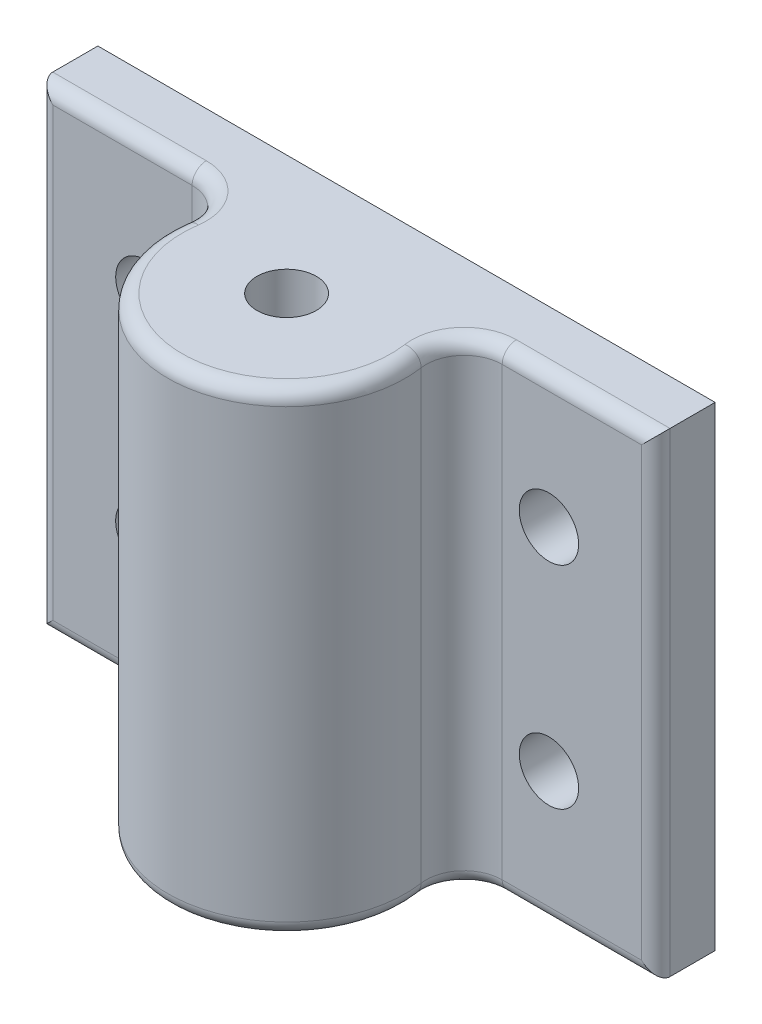
SolidWorks part; units mm, degrees
material "ABS"
ref_plane "Front Plane" through (0, 0, 0) normal (0, 0, 1) x (1, 0, 0)
ref_plane "Top Plane" through (0, 0, 0) normal (0, 1, 0) x (1, 0, 0)
ref_plane "Right Plane" through (0, 0, 0) normal (1, 0, 0) x (0, 0, -1)
sketch "Sketch1" plane through (0, 0, 0) normal (0, 1, 0) x (1, 0, 0)
  circle A0 centre (0, 0) radius 6.35
  dimension "D1" = 12.7
extrude "Boss-Extrude1" add sketch "Sketch1" along normal mid plane 25.4
sketch "Sketch2" plane through (0, -12.7, 0) normal (0, -1, 0) x (1, 0, 0)
  line L0 (0, 0) -> (0, -3.6102) construction
  line L1 (16.51, -3.2385) -> (-16.51, -3.2385)
  line L2 (16.51, -3.2385) -> (16.51, -6.4135)
  line L3 (16.51, -6.4135) -> (-16.51, -6.4135)
  line L4 (-16.51, -3.2385) -> (-16.51, -6.4135)
  line L5 (16.51, -3.2385) -> (-16.51, -6.4135) construction
  line L6 (16.51, -6.4135) -> (-16.51, -3.2385) construction
  line L7 (0, -6.4135) -> (0, -2.539) construction
  point P0 (0, -4.826)
  dimension "D1" = 33.02
  dimension "D2" = 3.175
  dimension "D3" = 4.826
extrude "Boss-Extrude2" add sketch "Sketch2" against normal blind 25.4 contours L3 L4 L1 L2
sketch "Sketch4" plane through (0, 0, -3.2385) normal (0, 0, 1) x (1, 0, 0)
  line L0 (0, 0) -> (0, 9.6957) construction
  line L1 (0, 0) -> (11.7503, 0) construction
  circle A0 centre (10.795, 5.6515) radius 1.5875
  circle A1 centre (10.795, -5.6515) radius 1.5875
  circle A2 centre (-10.795, -5.6515) radius 1.5875
  circle A3 centre (-10.795, 5.6515) radius 1.5875
  dimension "D1" = 3.175
  dimension "D2" = 11.303
  dimension "D3" = 21.59
extrude "Cut-Extrude1" cut sketch "Sketch4" against normal up to next
sketch "Sketch5" plane through (0, 12.7, 0) normal (0, 1, 0) x (1, 0, 0)
  circle A0 centre (0, 0) radius 1.5875
  dimension "D1" = 3.175
extrude "Cut-Extrude2" cut sketch "Sketch5" against normal blind 19.05
fillet "Fillet2" radius 2.032 2 edges at (-5.4621, 0, -3.2385) (5.4621, 0, -3.2385)
fillet "Fillet3" radius 0.762 12 edges at (-12.4024, -12.7, -3.2385) (-12.4024, 12.7, -3.2385) (-6.7579, -12.7, -2.5359) (12.4024, 12.7, -3.2385) (12.4024, -12.7, -3.2385) (6.7579, -12.7, -2.5359) (-6.7579, 12.7, -2.5359) (6.7579, 12.7, -2.5359) (0, -12.7, 6.35) (0, 12.7, 6.35) (16.51, 0, -3.2385) (-16.51, 0, -3.2385)
